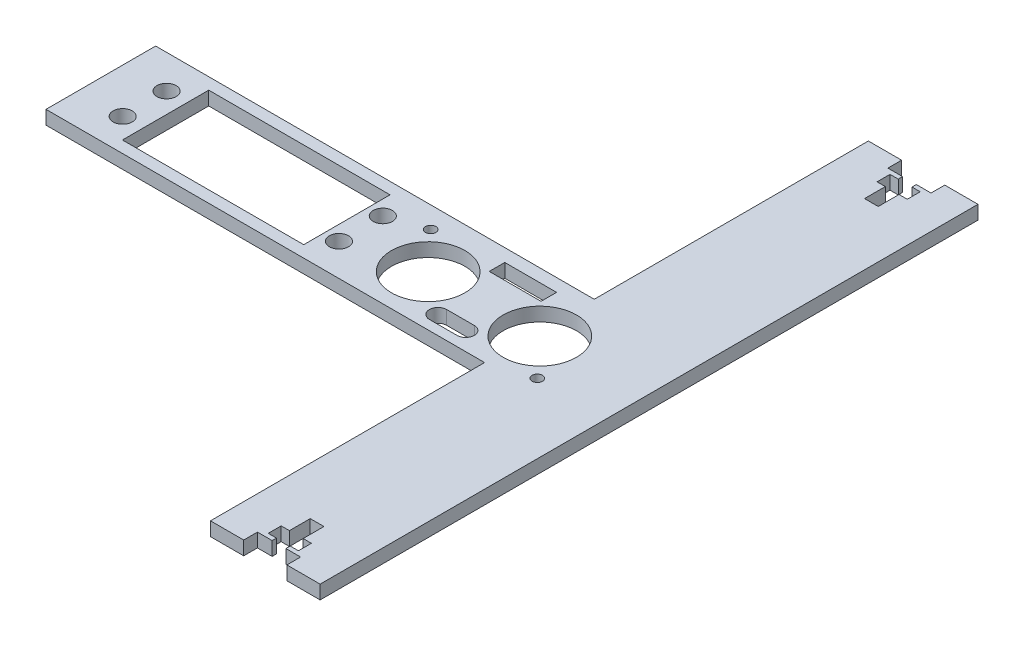
SolidWorks part; units mm, degrees
ref_plane "Front Plane" through (0, 0, 0) normal (0, 0, 1) x (1, 0, 0)
ref_plane "Top Plane" through (0, 0, 0) normal (0, 1, 0) x (1, 0, 0)
ref_plane "Right Plane" through (0, 0, 0) normal (1, 0, 0) x (0, 0, -1)
sketch "Sketch1" plane through (0, 0, 0) normal (0, 1, 0) x (1, 0, 0)
  line L0 (12.7, 0) -> (-114.3, 0) construction
  line L1 (12.7, 76.2) -> (-12.7, 76.2)
  line L2 (12.7, 76.2) -> (12.7, -76.2)
  line L3 (12.7, -76.2) -> (-12.7, -76.2)
  line L4 (-12.7, 76.2) -> (-12.7, 12.7)
  line L5 (12.7, 76.2) -> (-12.7, -76.2) construction
  line L6 (12.7, -76.2) -> (-12.7, 76.2) construction
  line L7 (-12.7, -12.7) -> (-114.3, -12.7)
  line L10 (-114.3, -12.7) -> (-114.3, 12.7)
  line L11 (-12.7, -12.7) -> (-12.7, -76.2)
  line L12 (-12.7, 12.7) -> (-114.3, 12.7)
  point P0 (0, 0)
  point P12 (0, 0)
  point P15 (12.7, -11.5456)
  point P16 (0, 0)
  point P17 (0, 0)
  dimension "D1" = 25.4
  dimension "D2" = 152.4
  dimension "D3" = 25.4
  dimension "D4" = 127
extrude "Boss-Extrude1" add sketch "Sketch1" along normal blind 3.18
sketch "Sketch2" plane through (0, 3.18, 0) normal (0, 1, 0) x (1, 0, 0)
  line L0 (12.7, 76.2) -> (-12.7, 76.2) construction
  line L2 (-1.59, 73.02) -> (-1.59, 72.02)
  line L4 (1.59, 73.02) -> (1.59, 72.02)
  line L5 (12.7, 0) -> (-114.3, 0) construction
  line L6 (1.59, 73.02) -> (5, 73.02)
  line L7 (-5, 76.2) -> (5, 76.2)
  line L8 (-5, 76.2) -> (-5, 73.02)
  line L9 (-5, 73.02) -> (-1.59, 73.02)
  line L10 (5, 76.2) -> (5, 73.02)
  line L11 (-3.5, 72.02) -> (-1.59, 72.02)
  line L12 (-3.5, 72.02) -> (-3.5, 69.02)
  line L13 (-3.5, 69.02) -> (-1.59, 69.02)
  line L14 (3.5, 72.02) -> (3.5, 69.02)
  line L15 (1.59, 72.02) -> (3.5, 72.02)
  line L16 (1.59, 69.02) -> (3.5, 69.02)
  line L17 (-1.59, 69.02) -> (-1.59, 64.2)
  line L18 (1.59, 69.02) -> (1.59, 64.2)
  line L19 (12.7, -76.2) -> (12.7, 76.2) construction
  line L20 (-114.3, 12.7) -> (-114.3, -12.7) construction
  line L21 (1.59, -72.02) -> (3.5, -72.02)
  line L40 (-3.5, -69.02) -> (-1.59, -69.02)
  line L41 (-1.59, 64.2) -> (1.59, 64.2)
  line L42 (-3.5, -72.02) -> (-3.5, -69.02)
  line L43 (-3.5, -72.02) -> (-1.59, -72.02)
  line L44 (5, -76.2) -> (5, -73.02)
  line L45 (-5, -73.02) -> (-1.59, -73.02)
  line L46 (-5, -76.2) -> (-5, -73.02)
  line L47 (-5, -76.2) -> (5, -76.2)
  line L48 (1.59, -73.02) -> (5, -73.02)
  line L49 (1.59, -73.02) -> (1.59, -72.02)
  line L50 (-1.59, -73.02) -> (-1.59, -72.02)
  line L51 (-1.59, -64.2) -> (1.59, -64.2)
  line L52 (1.59, -69.02) -> (1.59, -64.2)
  line L53 (-1.59, -69.02) -> (-1.59, -64.2)
  line L54 (1.59, -69.02) -> (3.5, -69.02)
  line L55 (3.5, -72.02) -> (3.5, -69.02)
  point P30 (0, 0)
  dimension "D1" = 3.18
  dimension "D2" = 12
  dimension "D3" = 10
  dimension "D4" = 3.18
  dimension "D5" = 1
  dimension "D6" = 7
  dimension "D7" = 3
extrude "Cut-Extrude1" cut sketch "Sketch2" against normal blind 3.18
sketch "Sketch3" plane through (0, 0, 0) normal (0, -1, 0) x (-1, 0, 0)
  line L0 (114.3, 0) -> (47.2726, 0) construction
  line L1 (114.3, 12.7) -> (114.3, -12.7) construction
  line L3 (99.3, -10) -> (57.3, -10)
  line L4 (99.3, -10) -> (99.3, 10)
  line L5 (99.3, 10) -> (57.3, 10)
  line L6 (57.3, -10) -> (57.3, 10)
  line L7 (99.3, -10) -> (57.3, 10) construction
  line L8 (99.3, 10) -> (57.3, -10) construction
  point P5 (78.3, 0)
  dimension "D1" = 20
  dimension "D2" = 42
  dimension "D3" = 15
extrude "Cut-Extrude2" cut sketch "Sketch3" against normal blind 10 contours L4 L5 L6 L3
sketch "Sketch4" plane through (0, 0, 0) normal (0, -1, 0) x (-1, 0, 0)
  circle A1 centre (103.999, -5.2375) radius 2.2225
  circle A2 centre (103.999, 4.9225) radius 2.2225
  circle A3 centre (53.901, 4.9225) radius 2.2225
  circle A4 centre (53.901, -5.2375) radius 2.2225
  dimension "D1" = 4.445
  dimension "D2" = 4.445
  dimension "D3" = 4.445
  dimension "D4" = 4.445
extrude "Cut-Extrude3" cut sketch "Sketch4" against normal blind 10
sketch "Sketch5" plane through (0, 0, 0) normal (0, -1, 0) x (1, 0, 0)
  line L0 (-27.7336, 10.4461) -> (-21.3336, 10.4461)
  line L1 (-27.7336, 6.4461) -> (-21.3336, 6.4461)
  line L3 (-18.4463, -6.1209) -> (-30.4463, -6.1209)
  line L4 (-18.4463, -6.1209) -> (-18.4463, -9.7218)
  line L5 (-18.4463, -9.7218) -> (-30.4463, -9.7218)
  line L6 (-30.4463, -6.1209) -> (-30.4463, -9.7218)
  line L7 (-18.4463, -6.1209) -> (-30.4463, -9.7218) construction
  line L8 (-18.4463, -9.7218) -> (-30.4463, -6.1209) construction
  circle A0 centre (-37.4675, 0.9961) radius 8.5
  circle A1 centre (-11.6075, 0.9961) radius 8.5
  arc A2 (-21.3336, 6.4461) -> (-21.3336, 10.4461) centre (-21.3336, 8.4461) ccw
  arc A3 (-27.7336, 10.4461) -> (-27.7336, 6.4461) centre (-27.7336, 8.4461) ccw
  point P7 (-24.4463, -7.9214)
  dimension "D1" = 4
  dimension "D2" = 4
  dimension "D3" = 17
  dimension "D4" = 17
  dimension "D5" = 6.4
  dimension "D6" = 6.4
  dimension "D7" = 12
  dimension "D8" = 3.6009
extrude "Cut-Extrude4" cut sketch "Sketch5" against normal blind 10
sketch "Sketch6" plane through (0, 3.18, 0) normal (0, 1, 0) x (1, 0, 0)
  circle A1 centre (-3.4375, -9.7461) radius 1.2
  circle A2 centre (-45.6375, 7.7539) radius 1.2
  dimension "D1" = 2.4
  dimension "D2" = 2.4
extrude "Cut-Extrude5" cut sketch "Sketch6" against normal blind 10 contours A2 | A1
